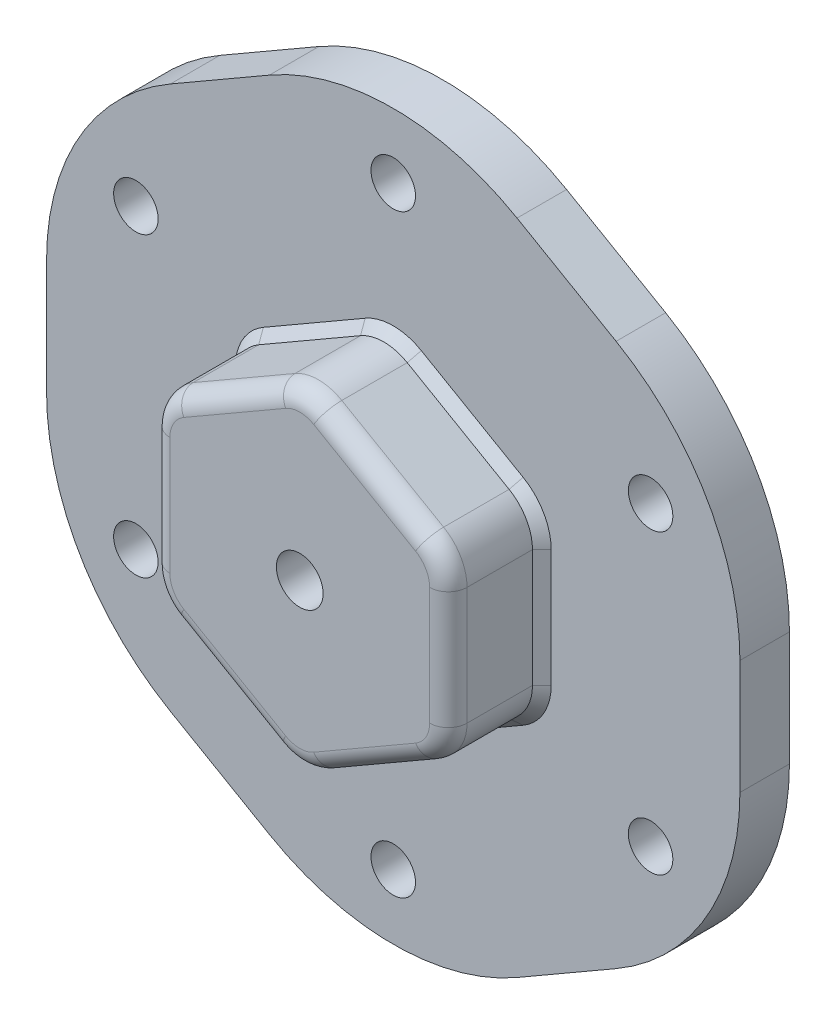
SolidWorks part; units mm, degrees
ref_plane "Front Plane" through (0, 0, 0) normal (0, 0, 1) x (1, 0, 0)
ref_plane "Top Plane" through (0, 0, 0) normal (0, 1, 0) x (1, 0, 0)
ref_plane "Right Plane" through (0, 0, 0) normal (1, 0, 0) x (0, 0, -1)
sketch "Sketch1" plane through (0, 0, 0) normal (0, 0, 1) x (1, 0, 0)
  line L1 (-13.245, 35.1763) -> (-23.8411, 29.0587)
  line L2 (-37.0861, 6.1176) -> (-37.0861, -6.1176)
  line L3 (-23.8411, -29.0587) -> (-13.245, -35.1763)
  line L4 (13.245, -35.1763) -> (23.8411, -29.0587)
  line L5 (37.0861, -6.1176) -> (37.0861, 6.1176)
  line L6 (23.8411, 29.0587) -> (13.245, 35.1763)
  circle A0 centre (0, 0) radius 37.0861 construction
  circle A1 centre (0, 0) radius 31.7881 construction
  circle A2 centre (0, 31.7881) radius 2.3812
  circle A3 centre (27.5293, 15.894) radius 2.3813
  circle A4 centre (27.5293, -15.894) radius 2.3813
  circle A5 centre (0, -31.7881) radius 2.3813
  circle A6 centre (-27.5293, -15.894) radius 2.3813
  circle A7 centre (-27.5293, 15.894) radius 2.3813
  arc A8 (37.0861, 6.1176) -> (23.8411, 29.0587) centre (10.596, 6.1176) ccw
  arc A9 (23.8411, -29.0587) -> (37.0861, -6.1176) centre (10.596, -6.1176) ccw
  arc A10 (-13.245, -35.1763) -> (13.245, -35.1763) centre (0, -12.2352) ccw
  arc A11 (-37.0861, -6.1176) -> (-23.8411, -29.0587) centre (-10.596, -6.1176) ccw
  arc A12 (-23.8411, 29.0587) -> (-37.0861, 6.1176) centre (-10.596, 6.1176) ccw
  arc A13 (-13.245, 35.1763) -> (13.245, 35.1763) centre (0, 12.2352) cw
  circle A14 centre (0, 0) radius 12.2352 construction
  point P27 (0, 0)
  dimension "D1" = 6
  dimension "D2" = 26.4901
  dimension "D3" = 4.7625
  dimension "D4" = 74.1722
  dimension "D5" = 63.5762
extrude "Boss-Extrude1" add sketch "Sketch1" along normal blind 5.298
sketch "Sketch3" plane through (0, 0, 5.298) normal (0, 0, 1) x (1, 0, 0)
  line L0 (0, 4.3199) -> (0, -6.0914) construction
  line L1 (-2.5, 16.9095) -> (-13.394, 10.6198)
  line L2 (-15.894, 6.2897) -> (-15.894, -6.2897)
  line L3 (-13.394, -10.6198) -> (-2.5, -16.9095)
  line L4 (2.5, -16.9095) -> (13.394, -10.6198)
  line L5 (15.894, -6.2897) -> (15.894, 6.2897)
  line L6 (13.394, 10.6198) -> (2.5, 16.9095)
  line L7 (-4.934, 0) -> (5.1039, 0) construction
  circle A0 centre (0, 0) radius 15.894 construction
  circle A1 centre (0, 0) radius 2.5
  arc A3 (15.894, 6.2897) -> (13.394, 10.6198) centre (10.894, 6.2897) ccw
  arc A4 (13.394, -10.6198) -> (15.894, -6.2897) centre (10.894, -6.2897) ccw
  arc A5 (-2.5, -16.9095) -> (2.5, -16.9095) centre (0, -12.5794) ccw
  arc A6 (-15.894, -6.2897) -> (-13.394, -10.6198) centre (-10.894, -6.2897) ccw
  arc A7 (-13.394, 10.6198) -> (-15.894, 6.2897) centre (-10.894, 6.2897) ccw
  arc A8 (-2.5, 16.9095) -> (2.5, 16.9095) centre (0, 12.5794) cw
  dimension "D1" = 5
  dimension "D2" = 31.7881
  dimension "D3" = 5
extrude "Boss-Extrude4" add sketch "Sketch3" along normal blind 10
chamfer "Chamfer2" distance 1 angle 45 12 edges at (7.947, 13.7646, 5.298) (15.894, 0, 5.298) (7.947, -13.7646, 5.298) (-7.947, -13.7646, 5.298) (-15.894, 0, 5.298) (-7.947, 13.7646, 5.298) (15.2242, -8.7897, 5.298) (0, -17.5794, 5.298) (15.2242, 8.7897, 5.298) (-15.2242, -8.7897, 5.298) (0, 17.5794, 5.298) (-15.2242, 8.7897, 5.298)
fillet "Fillet1" radius 2 12 edges at (15.2242, -8.7897, 15.298) (7.947, -13.7646, 15.298) (0, -17.5794, 15.298) (-7.947, -13.7646, 15.298) (-15.2242, -8.7897, 15.298) (-15.894, 0, 15.298) (-15.2242, 8.7897, 15.298) (-7.947, 13.7646, 15.298) (0, 17.5794, 15.298) (7.947, 13.7646, 15.298) (15.2242, 8.7897, 15.298) (15.894, 0, 15.298)
sketch "Croquis1" plane through (0, 0, 5.298) normal (0, 0, 1) x (1, 0, 0)
  circle A1 centre (0, 0) radius 2.5
  circle A2 centre (0, 0) radius 2.5
  dimension "D1" = 0
extrude "Cortar-Extruir1" cut sketch "Croquis1" against normal blind 10
